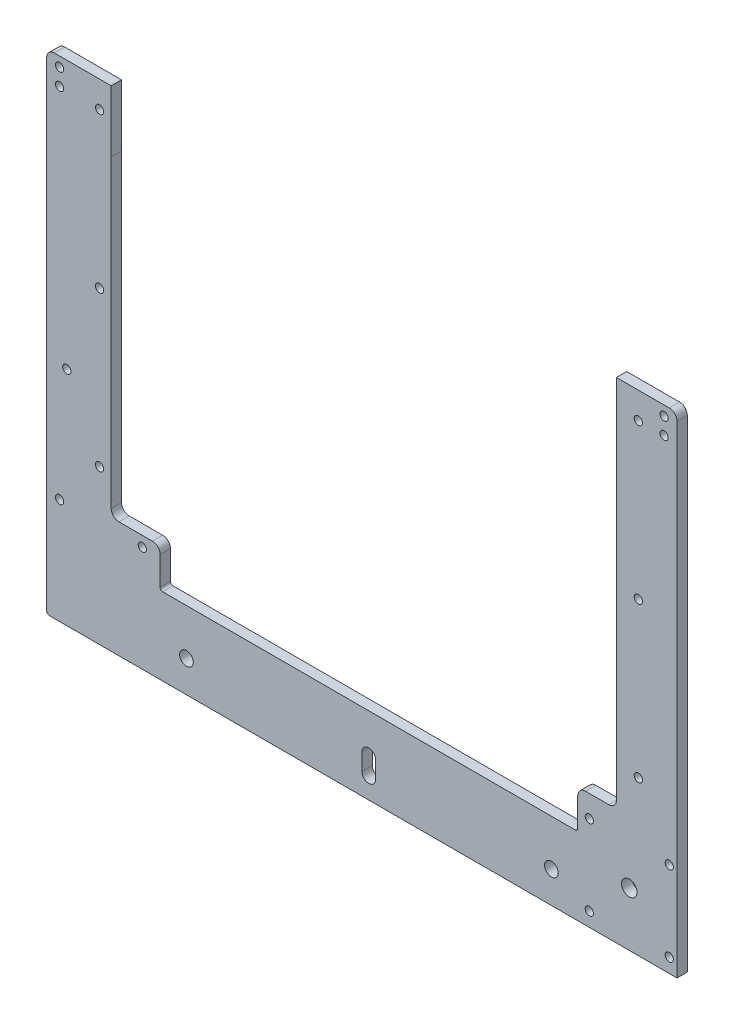
SolidWorks part; units mm, degrees
ref_plane "Plano frontal" through (0, 0, 0) normal (0, 0, 1) x (1, 0, 0)
ref_plane "Plano superior" through (0, 0, 0) normal (0, 1, 0) x (1, 0, 0)
ref_plane "Plano direito" through (0, 0, 0) normal (1, 0, 0) x (0, 0, -1)
sketch "Esboço1" plane through (0, 0, 0) normal (0, 0, 1) x (1, 0, 0)
  line L0 (-36.7564, -93.1156) -> (-55.7564, -93.1156)
  line L1 (-35.7564, -108.1156) -> (124.2436, -108.1156)
  line L2 (-55.7564, -79.1156) -> (-55.7564, 27.8844)
  line L3 (-52.7564, 30.8844) -> (141.2436, 30.8844)
  line L4 (144.2436, -79.1156) -> (144.2436, 27.8844)
  line L5 (168.2436, -138.1156) -> (-79.7564, -138.1156)
  line L6 (169.2436, -137.1156) -> (169.2436, 48.8844)
  line L7 (166.2436, 51.8844) -> (-77.7564, 51.8844)
  line L8 (-80.7564, -137.1156) -> (-80.7564, 48.8844)
  line L9 (44.2436, -142.1156) -> (44.2436, -132.526) construction
  line L10 (144.2436, -93.1156) -> (144.2436, -79.1156)
  line L11 (-36.7564, -93.1156) -> (-36.7564, -107.1156)
  line L12 (125.2436, -93.1156) -> (144.2436, -93.1156)
  line L13 (-36.7564, -93.1156) -> (-41.6564, -93.1156) construction
  line L15 (125.2436, -93.1156) -> (125.2436, -107.1156)
  line L17 (-55.7564, -93.1156) -> (-55.7564, -79.1156)
  arc A2 (141.2436, 30.8844) -> (144.2436, 27.8844) centre (141.2436, 27.8844) cw
  arc A3 (-55.7564, 27.8844) -> (-52.7564, 30.8844) centre (-52.7564, 27.8844) cw
  arc A4 (-77.7564, 51.8844) -> (-80.7564, 48.8844) centre (-77.7564, 48.8844) ccw
  arc A5 (169.2436, 48.8844) -> (166.2436, 51.8844) centre (166.2436, 48.8844) ccw
  arc A6 (-36.7564, -107.1156) -> (-35.7564, -108.1156) centre (-35.7564, -107.1156) ccw
  arc A7 (-79.7564, -138.1156) -> (-80.7564, -137.1156) centre (-79.7564, -137.1156) cw
  arc A9 (168.2436, -138.1156) -> (169.2436, -137.1156) centre (168.2436, -137.1156) ccw
  arc A12 (125.2436, -107.1156) -> (124.2436, -108.1156) centre (124.2436, -107.1156) cw
  dimension "D2" = 1
  dimension "D10" = 44
  dimension "D11" = 3
  dimension "D12" = 45
  dimension "D13" = 1
  dimension "D3" = 250
  dimension "D4" = 190
  dimension "D5" = 21
  dimension "D6" = 30
  dimension "D7" = 25
  dimension "D8" = 25
  dimension "D9" = 45
extrude "Ressalto-extrusão1" add sketch "Esboço1" along normal blind 4
fillet "Filete1" radius 3 4 edges at (144.2436, -93.1156, 2) (125.2436, -93.1156, 2) (-55.7564, -93.1156, 2) (-36.7564, -93.1156, 2)
hole_wizard "M3 Clearance Hole1" positions "Esboço11" profile "Esboço10" hole size "M3" standard "ISO" end condition through all
sketch "Esboço11" plane through (0, 0, 0) normal (0, 0, -1) x (-1, 0, 0)
  point P0 (-164.23, -97.103)
  point P12 (43.67, -97.103)
  point P15 (75.7428, -97.103)
sketch "Esboço10" plane through (164.23, -97.103, 0) normal (1, 0, 0) x (0, 1, 0)
  line L0 (0, 0) -> (0, 4)
  line L1 (0, 4) -> (1.6, 4)
  line L2 (1.6, 4) -> (1.6, 0)
  line L5 (1.6, 0) -> (0, 0)
  line L11 (0, -6.35) -> (0, 107.95) construction
  dimension "Thru Hole Dia." = 3.2
  dimension "Thru Hole Depth" = 4
sketch "Esboço16" plane through (0, 0, 4) normal (0, 0, 1) x (1, 0, 0)
  line L0 (150.0557, -138.1156) -> (169.2436, -138.1156) construction
  line L3 (-79.7564, -138.1156) -> (168.2436, -138.1156) construction
  line L5 (169.2436, -137.1156) -> (169.2436, 48.8844) construction
  line L6 (169.2436, -127.14) -> (169.2436, -138.1156) construction
hole_wizard "Furo com folga de M32" positions "Esboço19" profile "Esboço18" hole size "M3" standard "Ansi Metric" end condition through all
sketch "Esboço19" plane through (0, 0, 4) normal (0, 0, 1) x (1, 0, 0)
  point P14 (44.2436, 46.9871)
sketch "Esboço18" plane through (44.2436, 46.9871, 4) normal (1, 0, 0) x (0, -1, 0)
  line L0 (0, 0) -> (0, 4)
  line L1 (0, 4) -> (1.435, 4)
  line L2 (1.435, 4) -> (1.435, 0)
  line L5 (1.435, 0) -> (0, 0)
  line L11 (0, -6.35) -> (0, 107.95) construction
  dimension "Thru Hole Dia." = 2.87
  dimension "Thru Hole Depth" = 4
hole_wizard "M3 Clearance Hole2" positions "Sketch2" profile "Sketch1" hole size "M3" standard "ISO" end condition through all
sketch "Sketch2" plane through (0, 0, 4) normal (0, 0, 1) x (1, 0, 0)
  point P0 (161.5603, 35.4802)
  point P3 (161.5603, 4.4802)
sketch "Sketch1" plane through (161.5603, 35.4802, 4) normal (1, 0, 0) x (0, -1, 0)
  line L0 (0, 0) -> (0, 4)
  line L1 (0, 4) -> (1.6, 4)
  line L2 (1.6, 4) -> (1.6, 0)
  line L5 (1.6, 0) -> (0, 0)
  line L11 (0, -6.35) -> (0, 107.95) construction
  dimension "Thru Hole Dia." = 3.2
  dimension "Thru Hole Depth" = 4
sketch "Sketch3" plane through (0, 0, 4) normal (0, 0, 1) x (1, 0, 0)
  line L3 (44.2436, 30.8844) -> (44.2436, 18.6097) construction
  line L8 (141.2436, 30.8844) -> (-52.7564, 30.8844) construction
  line L9 (183.6742, -138.1156) -> (156.2436, -138.1156)
  line L10 (183.6742, 51.8844) -> (183.6742, -138.1156)
  line L11 (156.2436, 51.8844) -> (183.6742, 51.8844)
  line L12 (156.2436, -138.1156) -> (156.2436, 51.8844)
extrude "Cut-Extrude1" cut sketch "Sketch3" against normal blind 10
sketch "Sketch5" plane through (0, 0, 0) normal (0, 0, -1) x (-1, 0, 0)
  line L0 (-44.2436, 30.8844) -> (-44.2436, 20.8984) construction
  line L1 (-141.2436, 30.8844) -> (52.7564, 30.8844) construction
  line L2 (-145.2403, -97.5002) -> (-140.2436, -97.5002)
  line L3 (-145.2403, 30.8844) -> (-145.2403, -97.5002)
  line L4 (-141.2436, 30.8844) -> (52.7564, 30.8844) construction
  line L6 (-137.2442, 30.8844) -> (-145.2403, 30.8844)
  line L10 (-140.2436, 27.9415) -> (-140.2436, -97.5002)
  arc A0 (-137.2442, 30.8844) -> (-140.2436, 27.9415) centre (-137.2442, 27.8844) ccw
  dimension "D1" = 3
extrude "Boss-Extrude1" add sketch "Sketch5" against normal blind 4
fillet "Fillet3" radius 3 1 edges at (156.2436, 51.8844, 2)
sketch "Sketch10" plane through (0, 0, 0) normal (0, 0, -1) x (-1, 0, 0)
  line L0 (-156.2436, -138.1156) -> (-156.2436, 48.8844)
  line L1 (-156.2436, -138.1156) -> (-163.7436, -138.1156)
  line L4 (-150.0557, -138.1156) -> (-169.2436, -138.1156) construction
  line L6 (-163.7436, -138.1156) -> (-163.7436, 51.8844)
  line L10 (-163.7436, 51.8844) -> (-153.2436, 51.8844)
  arc A1 (-153.2436, 51.8844) -> (-156.2436, 48.8844) centre (-153.2436, 48.8844) ccw
extrude "Boss-Extrude3" add sketch "Sketch10" against normal blind 4
hole_wizard "M3 Clearance Hole4" positions "Sketch12" profile "Sketch11" hole size "M3" standard "ISO" end condition through all
sketch "Sketch12" plane through (0, 0, 0) normal (0, 0, -1) x (-1, 0, 0)
  point P0 (-160.7436, -101.6156)
  point P2 (-160.7436, -132.6156)
  point P5 (-129.7436, -132.6156)
  point P6 (-129.7436, -101.6156)
sketch "Sketch11" plane through (160.7436, -101.6156, 0) normal (1, 0, 0) x (0, 1, 0)
  line L0 (0, 0) -> (0, 4)
  line L1 (0, 4) -> (1.6, 4)
  line L2 (1.6, 4) -> (1.6, 0)
  line L5 (1.6, 0) -> (0, 0)
  line L11 (0, -6.35) -> (0, 107.95) construction
  dimension "Thru Hole Dia." = 3.2
  dimension "Thru Hole Depth" = 4
fillet "Fillet5" radius 3 2 edges at (163.7436, 51.8844, 2) (140.2436, -93.1156, 2)
hole_wizard "M5 Clearance Hole1" positions "Esboço15" profile "Esboço14" hole size "M5" standard "ISO" end condition through all
sketch "Esboço15" plane through (0, 0, 0) normal (0, 0, -1) x (-1, 0, 0)
  point P1 (-115.0336, -125.8856)
  point P3 (26.5464, -125.8856)
  point P4 (-44.1899, -129.8656)
sketch "Esboço14" plane through (115.0336, -125.8856, 0) normal (1, 0, 0) x (0, 1, 0)
  line L0 (0, 0) -> (0, 4)
  line L1 (0, 4) -> (2.65, 4)
  line L2 (2.65, 4) -> (2.65, 0)
  line L5 (2.65, 0) -> (0, 0)
  line L11 (0, -6.35) -> (0, 107.95) construction
  dimension "Thru Hole Dia." = 5.3
  dimension "Thru Hole Depth" = 4
sketch "Sketch15" plane through (0, 0, 0) normal (0, 0, -1) x (-1, 0, 0)
  circle A1 centre (-145.2436, -117.1156) radius 3
  point P0 (-145.2436, -117.1156)
  point P2 (-144.7712, -129.7569)
  point P4 (-145.2436, -117.1156)
  point P5 (-144.7712, -129.7569)
  dimension "D1" = 6
extrude "Cut-Extrude6" cut sketch "Sketch15" against normal through all
sketch "Sketch17" plane through (0, 0, 0) normal (0, 0, -1) x (-1, 0, 0)
  line L1 (-140.2436, 27.9415) -> (55.7564, 27.9415)
  line L2 (-140.2436, 27.9415) -> (-140.2436, 51.8844)
  line L3 (-140.2436, 51.8844) -> (55.7564, 51.8844)
  line L4 (55.7564, 27.9415) -> (55.7564, 51.8844)
extrude "Cut-Extrude8" cut sketch "Sketch17" against normal blind 5
sketch "Sketch23" plane through (0, 0, 4) normal (0, 0, 1) x (1, 0, 0)
  line L0 (-55.7564, 27.8844) -> (-55.7564, -90.1156) construction
  line L1 (-55.7564, -56.9456) -> (-19.6598, -56.9456)
  line L2 (-55.7564, -56.9456) -> (-55.7564, -46.9456)
  line L3 (-55.7564, -46.9456) -> (-19.6598, -46.9456)
  line L5 (-18.4098, -51.9456) -> (-16.0426, -51.9456) construction
  line L6 (-19.6598, 45.5544) -> (-55.7564, 45.5544)
  line L8 (-19.6598, 35.5544) -> (-55.7564, 35.5544)
  line L9 (-55.7564, 45.5544) -> (-55.7564, 35.5544)
  arc A1 (-19.6598, -50.6956) -> (-19.6598, -53.1956) centre (-19.6598, -51.9456) ccw construction
  arc A2 (-19.6598, 35.5544) -> (-19.6598, 45.5544) centre (-19.6598, 40.5544) ccw
  arc A3 (-19.6598, -56.9456) -> (-19.6598, -46.9456) centre (-19.6598, -51.9456) ccw
  dimension "D1" = 10
  dimension "10" = 10
extrude "Boss-Extrude4" [suppressed] add sketch "Sketch23" against normal up to surface (4 mm away)
hole_wizard "M3 Clearance Hole6" positions "Esboço3" profile "Esboço2" hole size "M3" standard "ISO" end condition through all
sketch "Esboço3" plane through (0, 0, 0) normal (0, 0, -1) x (-1, 0, 0)
  line L2 (-148.7436, -78.3479) -> (-148.7436, -20.0979) construction
  line L3 (-148.7436, -20.0979) -> (-148.7436, 41.6521) construction
  point P0 (-148.7436, -78.3479)
  point P3 (-148.7436, -18.3479)
  point P6 (-148.7436, 41.6521)
  point P15 (60.2564, 41.6521)
  point P16 (60.2564, -18.3479)
  point P17 (60.2564, -78.3479)
  point P32 (72.9598, -51.9456)
sketch "Esboço2" plane through (148.7436, -78.3479, 0) normal (1, 0, 0) x (0, 1, 0)
  line L0 (0, 0) -> (0, 4)
  line L1 (0, 4) -> (1.6, 4)
  line L2 (1.6, 4) -> (1.6, 0)
  line L5 (1.6, 0) -> (0, 0)
  line L11 (0, -6.35) -> (0, 107.95) construction
  dimension "Thru Hole Dia." = 3.2
  dimension "Thru Hole Depth" = 4
hole_wizard "M3 Clearance Hole5" positions "Sketch21" profile "Sketch18" hole size "M3" standard "ISO" end condition through all
sketch "Sketch21" plane through (0, 0, 4) normal (0, 0, 1) x (1, 0, 0)
  line L0 (-80.7564, 48.8844) -> (-80.7564, -137.1156) construction
  line L1 (163.7436, 48.8844) -> (163.7436, -138.1156) construction
  line L2 (-60.2564, 41.6521) -> (158.7436, 41.6521) construction
  point P0 (-75.7564, 41.6521)
  point P2 (-75.7564, 48.1521)
  point P4 (158.7436, 48.1521)
  point P6 (158.7436, 41.6521)
  dimension "D1" = 5
  dimension "D2" = 5
  dimension "D3" = 6.5
  dimension "D4" = 5
  dimension "D5" = 5
  dimension "D6" = 6.5
sketch "Sketch18" plane through (-75.7564, 41.6521, 4) normal (1, 0, 0) x (0, -1, 0)
  line L0 (0, 0) -> (0, 4)
  line L1 (0, 4) -> (1.6, 4)
  line L2 (1.6, 4) -> (1.6, 0)
  line L5 (1.6, 0) -> (0, 0)
  line L11 (0, -6.35) -> (0, 107.95) construction
  dimension "Thru Hole Dia." = 3.2
  dimension "Thru Hole Depth" = 4
sketch "Sketch22" plane through (0, 0, 0) normal (0, 0, -1) x (-1, 0, 0)
  line L0 (-44.1899, -129.8656) -> (-44.1899, -123.2156) construction
  line L2 (-46.8408, -129.8656) -> (-46.8408, -123.2156)
  line L3 (-41.539, -129.8656) -> (-41.539, -123.2156)
  arc A0 (-46.8408, -129.8656) -> (-41.539, -129.8656) centre (-44.1899, -129.8656) ccw
  arc A1 (-41.539, -123.2156) -> (-46.8408, -123.2156) centre (-44.1899, -123.2156) ccw
  point P5 (-44.1899, -126.5406)
extrude "Cut-Extrude9" cut sketch "Sketch22" against normal blind 4
fillet "Fillet6" [suppressed] radius 10
